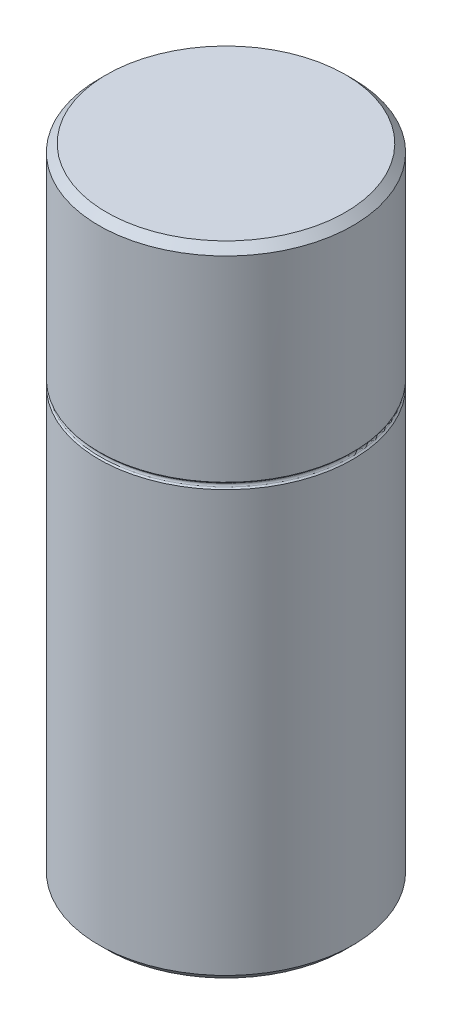
SolidWorks part; units mm, degrees
material "Brass"
ref_plane "Front" through (0, 0, 0) normal (0, 0, 1) x (1, 0, 0)
ref_plane "Top" through (0, 0, 0) normal (0, 1, 0) x (1, 0, 0)
ref_plane "Right" through (0, 0, 0) normal (1, 0, 0) x (0, 0, -1)
sketch "Sketch1" plane through (0, 0, 0) normal (0, 0, 1) x (1, 0, 0)
  line L0 (12.6365, 0.762) -> (12.6365, 62.738)
  line L1 (11.8745, 0) -> (6.3881, 0)
  line L2 (6.3881, 0) -> (6.3881, 4.572)
  line L3 (6.1341, 4.826) -> (0, 4.826)
  line L6 (0, 4.826) -> (0, 63.5)
  line L7 (11.8745, 63.5) -> (0, 63.5)
  line L8 (0, 0) -> (6.3881, 0) construction
  line L9 (0, 0) -> (0, 4.826) construction
  line L10 (6.3881, 4.572) -> (6.1341, 4.826)
  line L12 (12.6365, 62.738) -> (11.8745, 63.5)
  line L13 (12.6365, 0.762) -> (11.8745, 0)
  point P0 (12.6365, 0)
  point P1 (12.6365, 63.5)
  point P4 (6.3881, 4.826)
  dimension "D1" = 63.5
  dimension "D2" = 4.826
  dimension "D5" = 12.7762
  dimension "D6" = 25.273
  dimension "D9" = 0.254
  dimension "D11" = 0.762
  dimension "D12" = 0.762
revolve "Revolve1" add sketch "Sketch1" angle 360 about L9
sketch "Sketch2" plane through (0, 0, 0) normal (0, 0, 1) x (1, 0, 0)
  line L0 (-12.7, 42.926) -> (12.7, 42.926) construction
  line L1 (-11.8745, 0) -> (11.8745, 0) construction
  line L2 (0, 0) -> (0, 42.926) construction
  line L3 (12.7, 43.307) -> (12.7, 42.545)
  line L4 (12.7, 43.307) -> (12.4986, 43.1056)
  line L5 (12.7, 42.545) -> (12.4986, 42.7464)
  arc A0 (12.4986, 42.7464) -> (12.4986, 43.1056) centre (12.6782, 42.926) cw
  point P12 (12.319, 42.926)
  dimension "D5" = 0.254
  dimension "D1" = 42.926
  dimension "D2" = 25.4
  dimension "D3" = 0.762
  dimension "D4" = 45
revolve "Cut-Revolve1" cut sketch "Sketch2" angle 360 about L2
